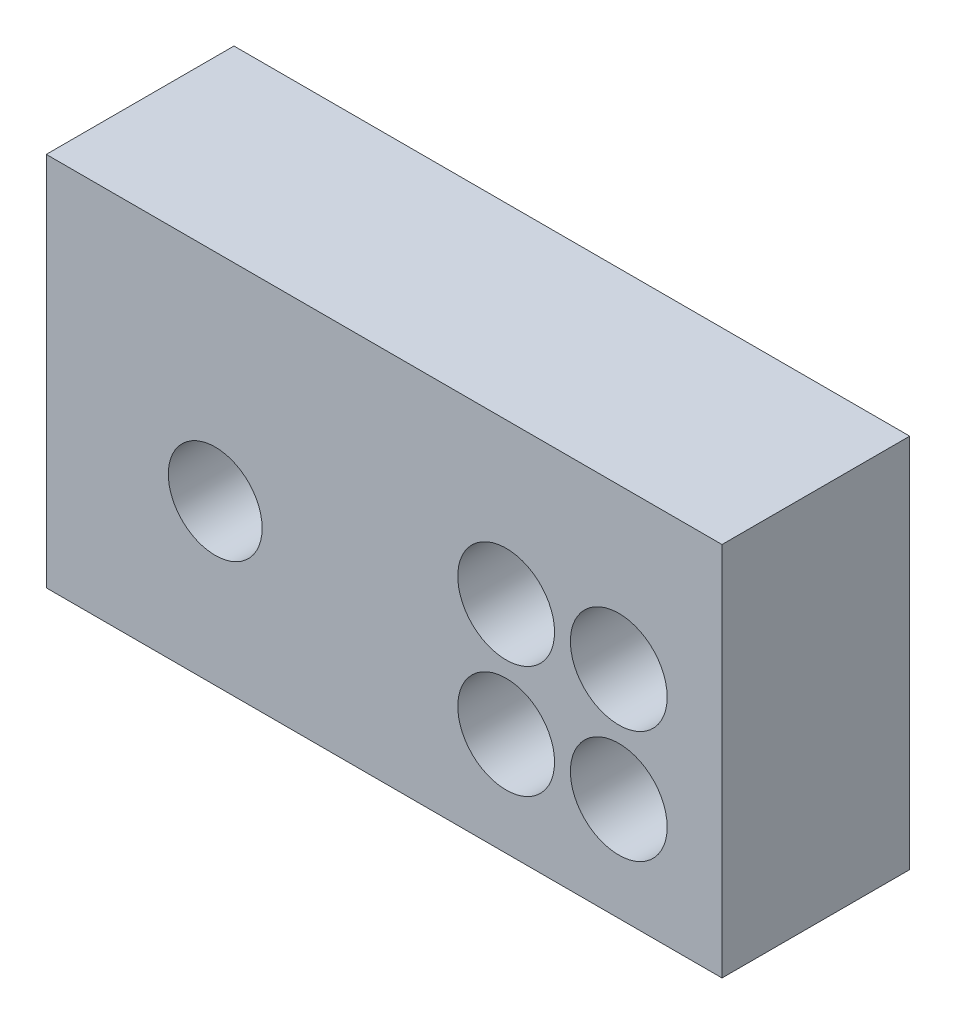
SolidWorks part; units mm, degrees
material "Custom Plastic"
ref_plane "Front Plane" through (0, 0, 0) normal (0, 0, 1) x (1, 0, 0)
ref_plane "Top Plane" through (0, 0, 0) normal (0, 1, 0) x (1, 0, 0)
ref_plane "Right Plane" through (0, 0, 0) normal (1, 0, 0) x (0, 0, -1)
sketch "Sketch1" plane through (0, 0, 0) normal (0, 0, 1) x (1, 0, 0)
  line L1 (-49.2709, 25.0565) -> (-45.6709, 25.0565)
  line L2 (-49.2709, 25.0565) -> (-49.2709, 23.0565)
  line L3 (-49.2709, 23.0565) -> (-45.6709, 23.0565)
  line L4 (-45.6709, 25.0565) -> (-45.6709, 23.0565)
  dimension "D1" = 3.6
  dimension "D2" = 2
extrude "Extrude1" add sketch "Sketch1" along normal blind 1
sketch "Sketch2" plane through (0, 0, 1) normal (0, 0, 1) x (1, 0, 0)
  line L0 (-49.2709, 23.0565) -> (-45.6709, 23.0565) construction
  line L2 (-49.2709, 25.0565) -> (-49.2709, 23.0565) construction
  circle A0 centre (-48.3709, 23.9065) radius 0.25
  dimension "D1" = 0.5
  dimension "D2" = 0.85
  dimension "D3" = 0.9
extrude "Cut-Extrude1" cut sketch "Sketch2" against normal through all
sketch "Sketch3" plane through (0, 0, 1) normal (0, 0, 1) x (1, 0, 0)
  line L5 (-49.2709, 23.0565) -> (-45.6709, 23.0565) construction
  line L7 (-45.6709, 23.0565) -> (-45.6709, 25.0565) construction
  circle A0 centre (-46.8209, 24.2065) radius 0.2578
  circle A1 centre (-46.8209, 23.6065) radius 0.2578
  circle A2 centre (-46.2209, 23.6065) radius 0.2578
  circle A3 centre (-46.2209, 24.2065) radius 0.2578
  dimension "D1" = 0.5156
  dimension "D2" = 0.6
  dimension "D3" = 0.6
  dimension "D4" = 0.55
  dimension "D5" = 0.55
extrude "Cut-Extrude2" cut sketch "Sketch3" against normal through all
